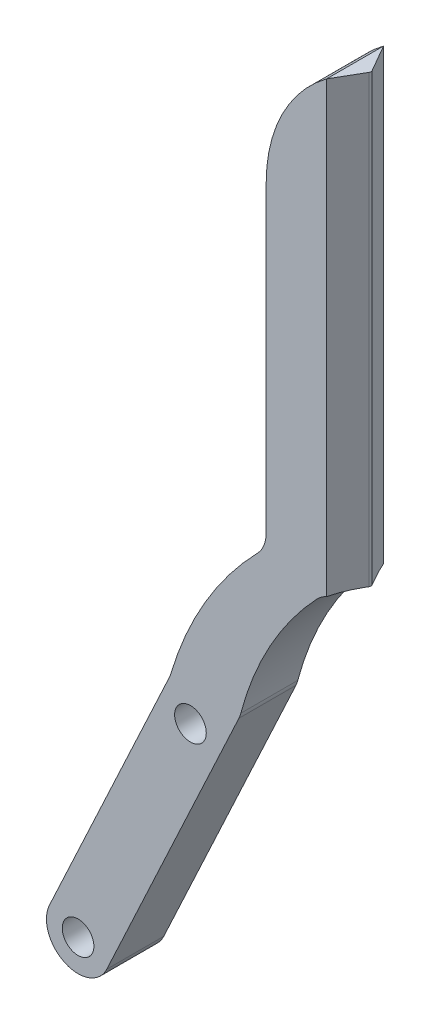
SolidWorks part; units mm, degrees
ref_plane "Front Plane" through (0, 0, 0) normal (0, 0, 1) x (1, 0, 0)
ref_plane "Top Plane" through (0, 0, 0) normal (0, 1, 0) x (1, 0, 0)
ref_plane "Right Plane" through (0, 0, 0) normal (1, 0, 0) x (0, 0, -1)
sketch "Sketch1" plane through (0, 0, 0) normal (0, 0, 1) x (1, 0, 0)
  line L0 (0, 0) -> (0, 124.6342) construction
  line L1 (0, 124.6342) -> (-11.0338, 124.6342) construction
  line L2 (-11.0338, 124.6342) -> (-11.0338, 0) construction
  line L3 (-11.0338, 0) -> (-30.1299, -40.9518)
  line L5 (-21.0669, -45.178) -> (0, 0)
  line L6 (-25.5984, -43.0649) -> (-7.8484, -5) construction
  line L7 (-11.0338, 0) -> (0, 0) construction
  line L8 (15.1516, 25) -> (15.1516, 95)
  line L9 (15.1516, 25) -> (4.1178, 25) construction
  line L10 (4.1178, 25) -> (4.1178, 75)
  arc A0 (-30.1299, -40.9518) -> (-21.0669, -45.178) centre (-25.5984, -43.0649) ccw
  circle A1 centre (-25.5984, -43.0649) radius 2.5
  circle A2 centre (-7.8484, -5) radius 2.5
  arc A3 (0, 0) -> (15.1516, 25) centre (48.4678, -12.2831) cw
  arc A4 (-11.0338, 0) -> (4.1178, 25) centre (43.1018, -15.7182) cw
  arc A5 (4.1178, 75) -> (15.1516, 95) centre (27.7608, 75) cw
  dimension "D2" = 5
  dimension "D3" = 5
  dimension "D10" = 50
  dimension "D1" = 155
  dimension "D4" = 42
  dimension "D5" = 5
  dimension "D6" = 23
  dimension "D7" = 100
  dimension "D8" = 50
  dimension "D9" = 25
extrude "Boss-Extrude1" add sketch "Sketch1" along normal blind 9
sketch "Sketch2" plane through (0, 0, 9) normal (0, 0, 1) x (1, 0, 0)
  line L1 (15.1516, 95) -> (13.6516, 95)
  line L2 (15.1516, 95) -> (15.1516, 23.6033)
  line L3 (15.1516, 23.6033) -> (13.6516, 23.6033)
  line L4 (13.6516, 95) -> (13.6516, 23.6033)
  arc A0 (15.1516, 25) -> (0, 0) centre (48.4678, -12.2831) ccw construction
  point P8 (13.6508, 23.6026)
  dimension "D1" = 1.5
extrude "Cut-Extrude1" cut sketch "Sketch2" against normal through all
ref_plane "Plane1" through (0, 93.9716, 0) normal (0, -1, 0) x (0, 0, -1)
sketch "Sketch4" plane through (0, 93.9716, 0) normal (0, -1, 0) x (0, 0, -1)
  line L0 (0, 13.6516) -> (-4.5, 16.2496)
  line L1 (-4.5, 16.2496) -> (-9, 13.6516)
  line L2 (-9, 13.6516) -> (0, 13.6516)
  line L3 (-4.5, 13.6516) -> (-4.5, 16.2496) construction
  point P6 (-4.5, 17.1765)
  dimension "D1" = 120
extrude "Boss-Extrude2" add sketch "Sketch4" along normal up to vertex (70.3684 mm away)
fillet "Fillet1" radius 0.5 1 edges at (16.2496, 58.7874, 4.5)
fillet "Fillet2" radius 5 4 edges at (0, 0, 4.5) (13.6516, 23.6033, 4.5) (-11.0338, 0, 4.5) (4.1178, 25, 4.5)
